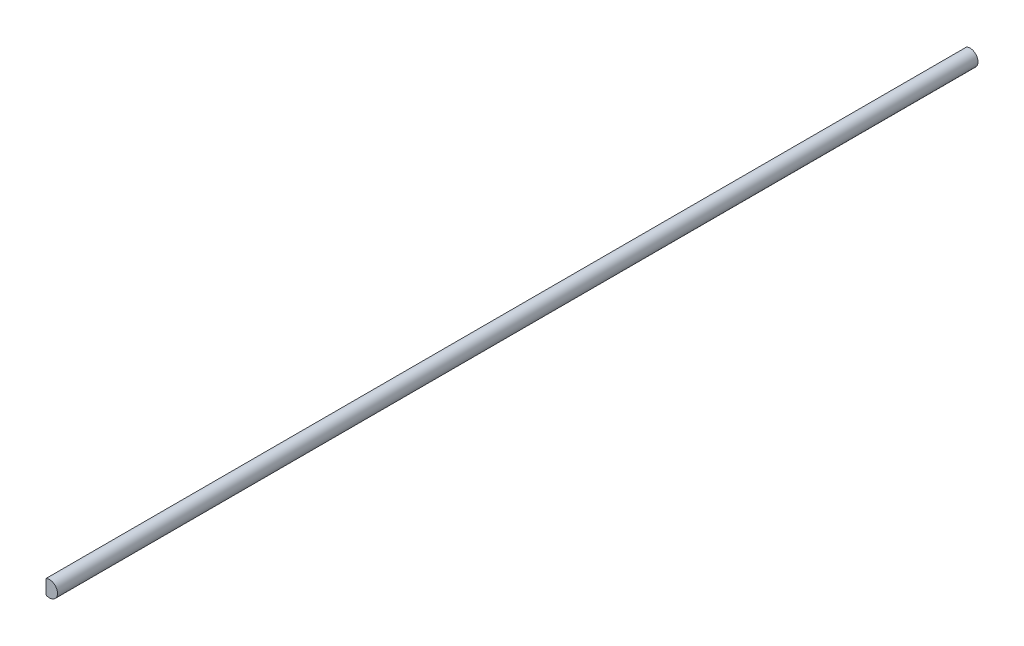
SolidWorks part; units mm, degrees
ref_plane "Front Plane" through (0, 0, 0) normal (0, 0, 1) x (1, 0, 0)
ref_plane "Top Plane" through (0, 0, 0) normal (0, 1, 0) x (1, 0, 0)
ref_plane "Right Plane" through (0, 0, 0) normal (1, 0, 0) x (0, 0, -1)
sketch "Sketch1" plane through (0, 0, 0) normal (0, 0, 1) x (1, 0, 0)
  line L2 (-0.99, 2.0205) -> (-0.99, -2.0205)
  arc A0 (-0.99, -2.0205) -> (-0.99, 2.0205) centre (0, 0) ccw
  point P4 (2.25, 0)
  dimension "D1" = 4.5
  dimension "D2" = 3.24
extrude "Boss-Extrude1" add sketch "Sketch1" along normal mid plane 260
